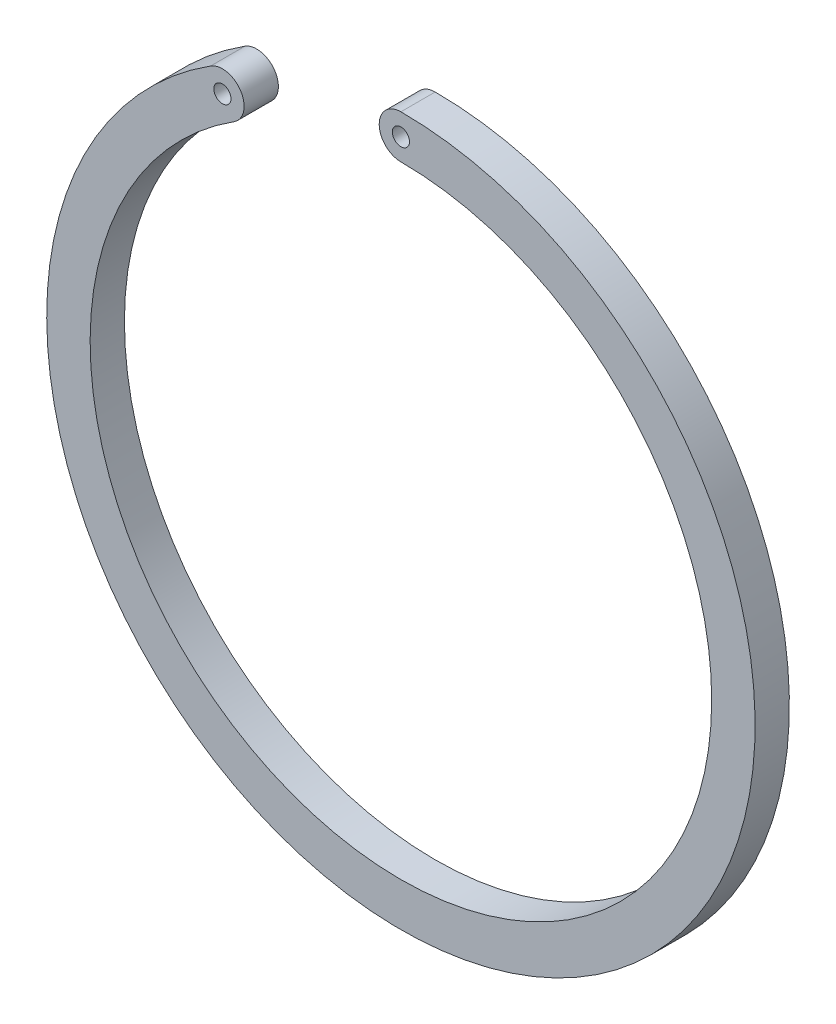
SolidWorks part; units mm, degrees
ref_plane "Front Plane" through (0, 0, 0) normal (0, 0, 1) x (1, 0, 0)
ref_plane "Top Plane" through (0, 0, 0) normal (0, 1, 0) x (1, 0, 0)
ref_plane "Right Plane" through (0, 0, 0) normal (1, 0, 0) x (0, 0, -1)
sketch "Sketch1" plane through (0, 0, 0) normal (0, 0, 1) x (1, 0, 0)
  circle A0 centre (0, 0) radius 27.2
  arc A1 (-16.6444, 26.1527) -> (0, 31) centre (0, 0) ccw
  arc A2 (0, 27.2) -> (0, 31) centre (0, 29.1) cw
  arc A3 (-14.6041, 22.9469) -> (-16.6444, 26.1527) centre (-15.6243, 24.5498) ccw
  circle A4 centre (-15.6243, 24.5498) radius 0.75
  circle A5 centre (0, 29.1) radius 0.75
  circle A6 centre (0, 0) radius 31 construction
  dimension "D1" = 62
  dimension "D3" = 1.5
  dimension "D2" = 3.8
extrude "Boss-Extrude1" add sketch "Sketch1" along normal blind 3 contours A0 A3 A1 A2 A5 A4
